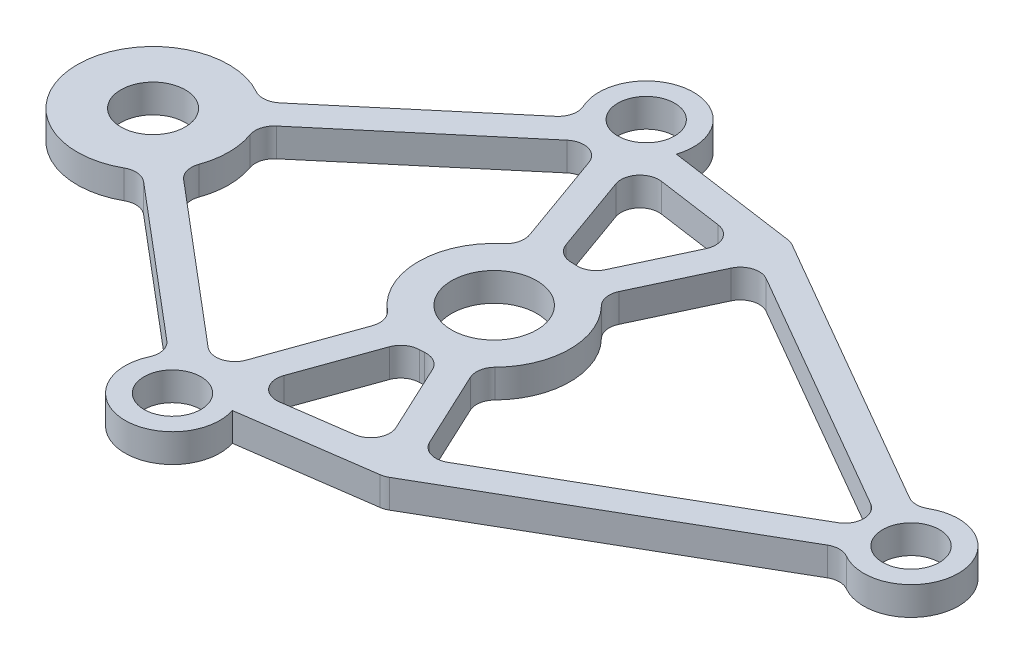
SolidWorks part; units mm, degrees
material "1060 Alloy"
ref_plane "Front" through (0, 0, 0) normal (0, 0, 1) x (1, 0, 0)
ref_plane "Top" through (0, 0, 0) normal (0, 1, 0) x (1, 0, 0)
ref_plane "Right" through (0, 0, 0) normal (1, 0, 0) x (0, 0, -1)
sketch "草图1" plane through (0, 0, 0) normal (0, 1, 0) x (1, 0, 0)
  line L0 (0, 0) -> (-18, 0) construction
  line L1 (0, 0) -> (22, 0) construction
  line L2 (22, 0) -> (4.6795, 10) construction
  line L4 (22, 0) -> (-4.4758, 12.5) construction
  line L6 (0.1065, -1.9972) -> (0.0924, -1.9669)
  line L7 (0.0811, -1.9984) -> (0.0924, -1.9669)
  line L8 (19.75, 2.1651) -> (5.0965, 10.6253)
  line L9 (4.7364, 10.7494) -> (-2.1019, 11.7159)
  line L10 (2.2314, 9.5886) -> (-1.2565, 10.0815)
  line L11 (4.9285, 10.7223) -> (-3.2584, 11.8794) construction
  line L12 (-7.0068, 10.2659) -> (-14.9056, 3.5951)
  line L13 (19, 0.866) -> (5.9562, 8.3969)
  line L14 (4.5504, -7.9547) -> (2.6645, -3.9244)
  line L15 (-2.3379, -8.7543) -> (-0.8728, -4.6624)
  line L16 (2.9972, 8.1746) -> (1.3059, 4.5601)
  line L17 (-5.6221, 9.4721) -> (-13.9377, 2.4491)
  line L18 (-3.2584, 11.8794) -> (-4.5001, 14.0565) construction
  line L19 (-4.0354, -9.0452) -> (-2.285, -4.1568)
  line L20 (-4.5001, 14.0565) -> (-6.1038, 11.0285) construction
  line L21 (-4.9142, 10.0699) -> (-17.5161, -0.573) construction
  line L22 (-6.1038, 11.0285) -> (-18.4839, 0.573) construction
  line L23 (21.625, -0.6495) -> (4.4305, 9.2777) construction
  line L24 (22.375, 0.6495) -> (4.9285, 10.7223) construction
  line L25 (-5.6221, -9.4721) -> (-13.9377, -2.4491)
  line L27 (-4.4515, 10.9435) -> (-4.9142, 10.0699) construction
  line L28 (2.9972, -8.1746) -> (1.3059, -4.5601)
  line L29 (4.4305, 9.2777) -> (-4.1969, 10.4971) construction
  line L30 (19, -0.866) -> (5.9562, -8.3969)
  line L31 (-4.0354, 9.0452) -> (-2.285, 4.1568)
  line L32 (-7.0068, -10.2659) -> (-14.9056, -3.5951)
  line L33 (-2.3379, 8.7543) -> (-0.8728, 4.6624)
  line L34 (2.2314, -9.5886) -> (-1.2565, -10.0815)
  line L35 (4.5504, 7.9547) -> (2.6645, 3.9244)
  line L38 (4.7364, -10.7494) -> (-2.1019, -11.7159)
  line L39 (19.75, -2.1651) -> (5.0965, -10.6253)
  line L41 (-4.1969, 10.4971) -> (-4.4515, 10.9435) construction
  line L42 (-3.7277, 11.1883) -> (-4.4758, 12.5) construction
  line L43 (-4.4758, 12.5) -> (-5.509, 10.5492) construction
  line L44 (4.6795, 10) -> (-3.7277, 11.1883) construction
  line L45 (-5.509, 10.5492) -> (-18, 0) construction
  circle A0 centre (0, 0) radius 2.25
  arc A1 (0.3201, 3.9872) -> (0.0549, 3.9996) centre (0, 0) ccw
  circle A2 centre (-18, 0) radius 1.7
  arc A3 (-16.0406, 3.4872) -> (-16.0406, -3.4872) centre (-18, 0) ccw
  circle A4 centre (22, 0) radius 1.5
  arc A5 (20.75, -2.1651) -> (20.75, 2.1651) centre (22, 0) ccw
  arc A7 (-2.5812, 3.0557) -> (-2.5812, -3.0557) centre (0, 0) ccw
  arc A8 (-2.1019, 11.7159) -> (-6.7446, 11.4499) centre (-4.4758, 12.5) ccw
  circle A9 centre (-4.4758, 12.5) radius 1.5
  arc A10 (19.75, 2.1651) -> (20.75, 2.1651) centre (20.25, 3.0311) ccw
  arc A11 (19, 0.866) -> (19, -0.866) centre (18.5, 0) cw
  arc A12 (-13.9377, 2.4491) -> (-14.234, 1.3481) centre (-13.2925, 1.6851) ccw
  arc A13 (-14.9056, 3.5951) -> (-16.0406, 3.4872) centre (-15.5508, 4.3591) cw
  arc A14 (-7.0068, 10.2659) -> (-6.7446, 11.4499) centre (-7.6521, 11.0299) ccw
  arc A15 (-2.285, 4.1568) -> (-2.5812, 3.0557) centre (-3.2265, 3.8197) cw
  arc A16 (2.8562, 2.8004) -> (2.6645, 3.9244) centre (3.5702, 3.5005) cw
  arc A17 (0.3201, 3.9872) -> (1.3059, 4.5601) centre (0.4001, 4.984) ccw
  arc A18 (-0.8728, 4.6624) -> (0.0549, 3.9996) centre (0.0687, 4.9995) ccw
  arc A19 (4.5504, 7.9547) -> (5.9562, 8.3969) centre (5.4562, 7.5309) cw
  arc A20 (5.0965, 10.6253) -> (4.7364, 10.7494) centre (4.5965, 9.7592) ccw
  arc A21 (2.2314, 9.5886) -> (2.9972, 8.1746) centre (2.0915, 8.5984) cw
  arc A22 (-1.2565, 10.0815) -> (-2.3379, 8.7543) centre (-1.3965, 9.0914) ccw
  arc A23 (-4.0354, 9.0452) -> (-5.6221, 9.4721) centre (-4.9768, 8.7081) ccw
  arc A24 (2.8562, -2.8004) -> (2.8562, 2.8004) centre (0, 0) ccw
  arc A25 (-14.234, -1.3481) -> (-14.234, 1.3481) centre (-18, 0) ccw
  arc A26 (-4.0354, -9.0452) -> (-5.6221, -9.4721) centre (-4.9768, -8.7081) cw
  arc A27 (-1.2565, -10.0815) -> (-2.3379, -8.7543) centre (-1.3965, -9.0914) cw
  arc A28 (2.2314, -9.5886) -> (2.9972, -8.1746) centre (2.0915, -8.5984) ccw
  arc A29 (5.0965, -10.6253) -> (4.7364, -10.7494) centre (4.5965, -9.7592) cw
  arc A30 (4.5504, -7.9547) -> (5.9562, -8.3969) centre (5.4562, -7.5309) ccw
  arc A31 (-0.8728, -4.6624) -> (0.0549, -3.9996) centre (0.0687, -4.9995) cw
  arc A32 (0.3201, -3.9872) -> (1.3059, -4.5601) centre (0.4001, -4.984) cw
  arc A33 (2.8562, -2.8004) -> (2.6645, -3.9244) centre (3.5702, -3.5005) ccw
  arc A34 (-2.285, -4.1568) -> (-2.5812, -3.0557) centre (-3.2265, -3.8197) ccw
  arc A35 (-7.0068, -10.2659) -> (-6.7446, -11.4499) centre (-7.6521, -11.0299) cw
  arc A36 (-14.9056, -3.5951) -> (-16.0406, -3.4872) centre (-15.5508, -4.3591) ccw
  arc A37 (-13.9377, -2.4491) -> (-14.234, -1.3481) centre (-13.2925, -1.6851) cw
  arc A38 (19.75, -2.1651) -> (20.75, -2.1651) centre (20.25, -3.0311) cw
  circle A39 centre (-4.4758, -12.5) radius 1.5
  arc A40 (-2.1019, -11.7159) -> (-6.7446, -11.4499) centre (-4.4758, -12.5) cw
  arc A41 (0.3201, -3.9872) -> (0.0549, -3.9996) centre (0, 0) cw
  point P53 (-2.0306, 3.4463)
  point P79 (-2.0306, -3.4463)
  dimension "D1" = 30
  dimension "D2" = 0.75
  dimension "D4" = 1
  dimension "D6" = 4.5
  dimension "D7" = 3.4
  dimension "D5" = 25.273
  dimension "D3" = 0.75
extrude "凸台-拉伸1" add sketch "草图1" along normal blind 1.5 contours A40 L38 A29 L39 A38 A5 A10 L8 A20 L9 A8 A14 L12 A13 A3 A36 L32 A35 A41 A32 L28 A28 L34 A27 L15 A31 L25 A37 A25 A12 L17 A23 L31 A15 A7 A34 L19 A26 A0 A2 A4 A9 A22
